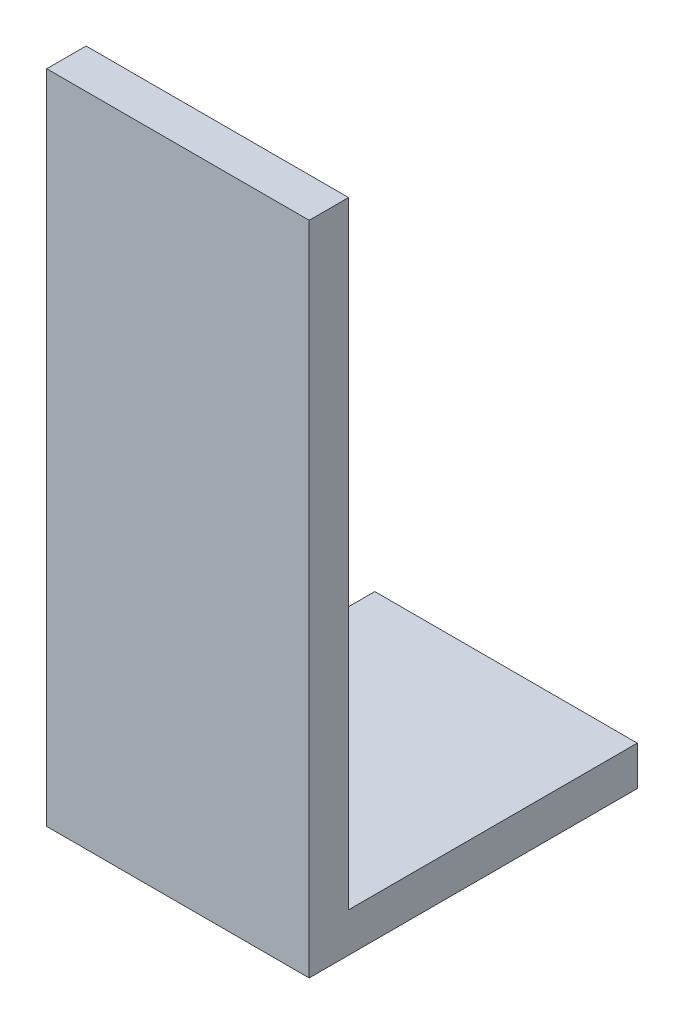
SolidWorks part; units mm, degrees
ref_plane "正面" through (0, 0, 0) normal (0, 0, 1) x (1, 0, 0)
ref_plane "平面" through (0, 0, 0) normal (0, 1, 0) x (1, 0, 0)
ref_plane "右側面" through (0, 0, 0) normal (1, 0, 0) x (0, 0, -1)
sketch "ｽｹｯﾁ1" plane through (0, 0, 0) normal (1, 0, 0) x (0, 0, -1)
  line L1 (0, 50) -> (3, 50)
  line L2 (0, 50) -> (0, 0)
  line L3 (0, 0) -> (3, 0)
  line L4 (3, 50) -> (3, 0)
  line L5 (0, 50) -> (3, 0) construction
  line L6 (0, 0) -> (3, 50) construction
  line L7 (0, 0) -> (25, 0)
  line L8 (0, 0) -> (0, 3)
  line L9 (0, 3) -> (25, 3)
  line L10 (25, 0) -> (25, 3)
  line L11 (0, 0) -> (25, 3) construction
  line L12 (0, 3) -> (25, 0) construction
  point P0 (1.5, 25)
  point P5 (12.5, 1.5)
  point P10 (0, 0)
  point P11 (0, 0)
  dimension "D1" = 50
  dimension "D2" = 25
  dimension "D3" = 3
  dimension "D4" = 3
extrude "ﾎﾞｽ - 押し出し1" add sketch "ｽｹｯﾁ1" along normal blind 20 contours L2 L9 L4 L1 | L9 L2 L3 L4 | L7 L10 L9 L4
